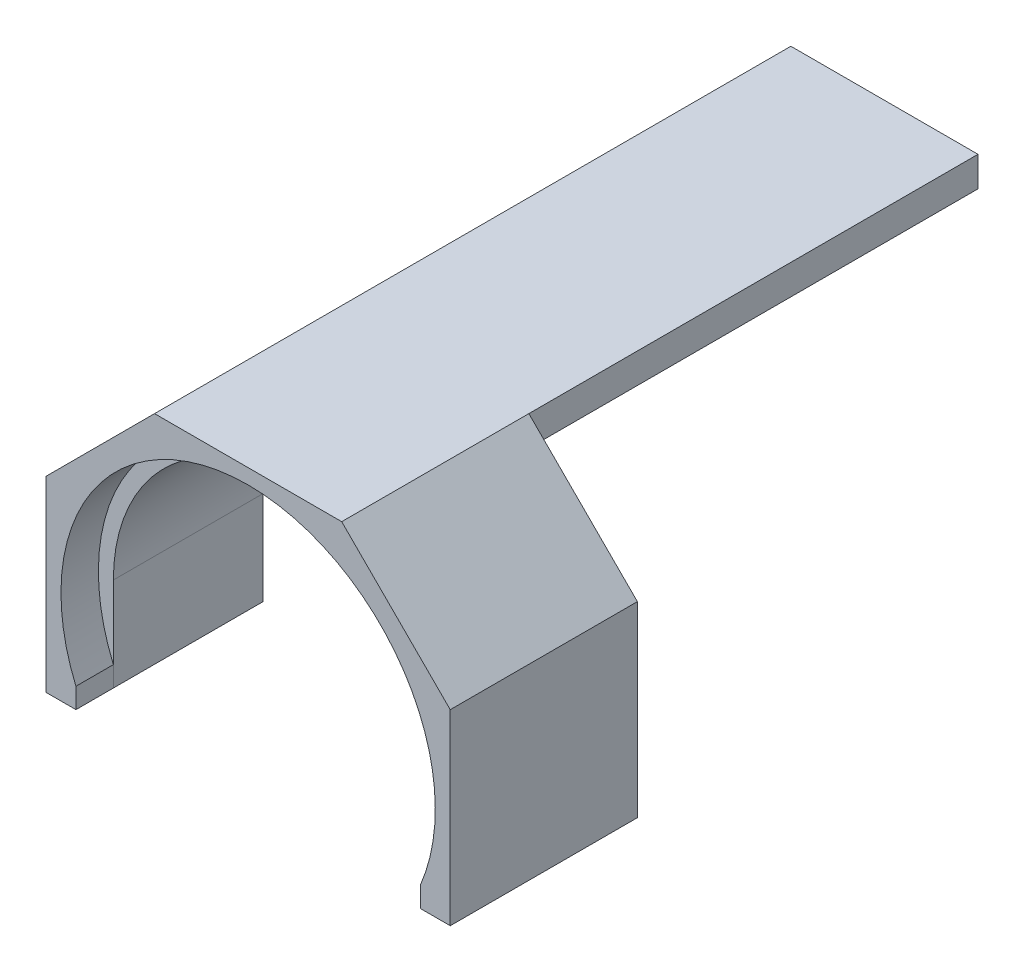
SolidWorks part; units mm, degrees
ref_plane "前视基准面" through (0, 0, 0) normal (0, 0, 1) x (1, 0, 0)
ref_plane "上视基准面" through (0, 0, 0) normal (0, 1, 0) x (1, 0, 0)
ref_plane "右视基准面" through (0, 0, 0) normal (1, 0, 0) x (0, 0, -1)
sketch "草图1" plane through (0, 0, 0) normal (0, 0, 1) x (1, 0, 0)
  line L0 (-39.8017, 0) -> (0, 0) construction
  line L1 (0, 0) -> (0, 40.2975) construction
  line L3 (-25, 4) -> (25, 4)
  line L4 (-25, 4) -> (-25, -4)
  line L5 (-25, -4) -> (25, -4)
  line L6 (25, 4) -> (25, -4)
  dimension "D1" = 50
  dimension "D2" = 25
  dimension "D3" = 8
  dimension "D4" = 4
sketch "草图2" plane through (0, 0, 0) normal (1, 0, 0) x (0, 0, -1)
  line L0 (0, 55.2983) -> (-160, 55.2983)
  line L1 (0, 4) -> (0, -4) construction
  line L2 (0, 4) -> (0, -4) construction
sweep "扫描1" add profiles "草图1" path "草图2"
sketch "草图4" plane through (0, 0, 160) normal (0, 0, 1) x (1, 0, 0)
  line L0 (0, -4) -> (0, -65.5134) construction
  line L4 (-25, -4) -> (25, -4) construction
  line L5 (-44.7277, -50) -> (-40, -50) construction
  line L6 (-54, -25) -> (-25, 4)
  line L8 (-54, -25) -> (-54, -75)
  line L14 (54, -25) -> (54, -75)
  line L15 (-25, 4) -> (25, 4)
  line L16 (25, 4) -> (54, -25)
  line L17 (-36, -50) -> (36, -50) construction
  line L19 (-46, -50) -> (-46, -75)
  line L20 (46, -50) -> (46, -75)
  line L21 (-54, -75) -> (-46, -75)
  line L22 (46, -75) -> (54, -75)
  arc A4 (46, -50) -> (-46, -50) centre (0, -50) ccw
  dimension "D2" = 50
  dimension "D1" = 25
  dimension "D3" = 8
  dimension "D4" = 8
  dimension "D5" = 50
extrude "凸台-拉伸1" add sketch "草图4" against normal blind 40
sketch "草图5" plane through (0, 0, 160) normal (0, 0, 1) x (1, 0, 0)
  line L0 (-46.0047, -69.585) -> (-46, -75)
  line L1 (-46, -75) -> (-54, -75)
  line L2 (-54, -75) -> (-54, -25)
  line L3 (-54, -25) -> (-25, 4)
  line L4 (-25, 4) -> (25, 4)
  line L5 (25, 4) -> (54, -25)
  line L6 (54, -25) -> (54, -75)
  line L7 (54, -75) -> (54, -25) construction
  line L8 (46, -75) -> (54, -75) construction
  line L9 (54, -75) -> (46, -75)
  line L10 (46, -50) -> (46, -75) construction
  line L11 (46, -69.5959) -> (46, -75)
  arc A0 (46, -69.5959) -> (-46.0047, -69.585) centre (0, -50) ccw
  point P3 (-46.0047, -69.585)
  point P24 (46, -69.5959)
extrude "凸台-拉伸2" add sketch "草图5" along normal blind 10
